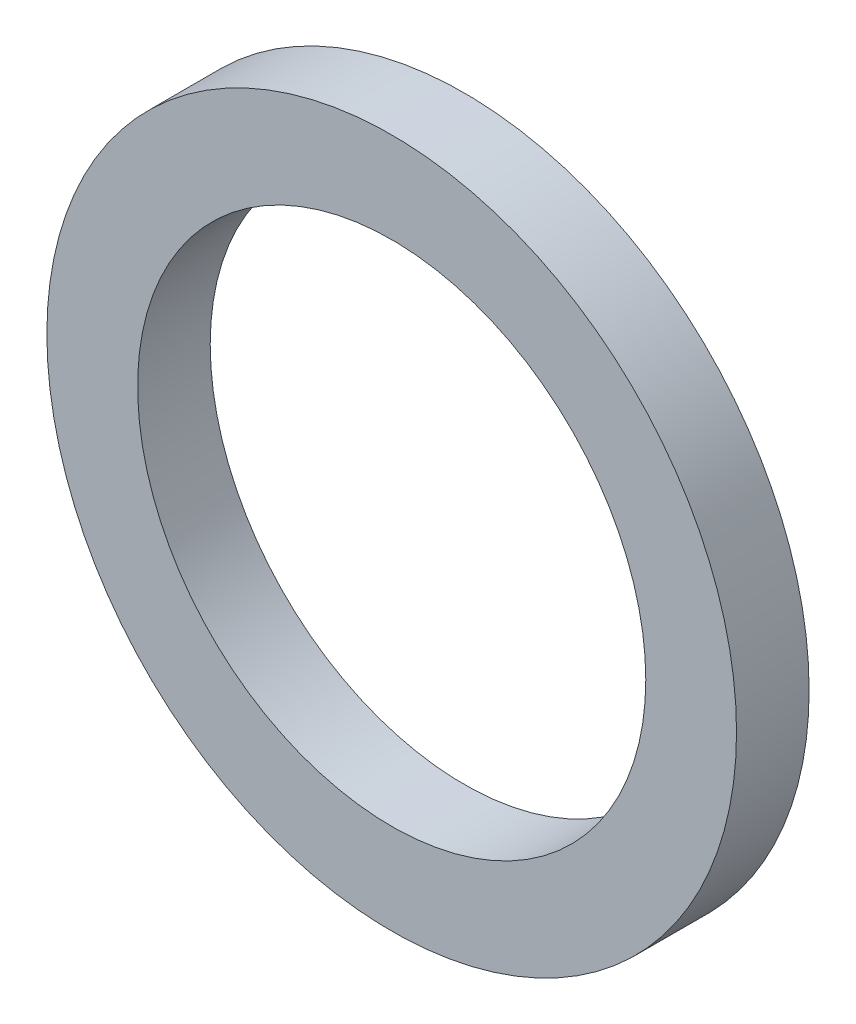
SolidWorks part; units mm, degrees
ref_plane "Plan de face" through (0, 0, 0) normal (0, 0, 1) x (1, 0, 0)
ref_plane "Plan de dessus" through (0, 0, 0) normal (0, 1, 0) x (1, 0, 0)
ref_plane "Plan de droite" through (0, 0, 0) normal (1, 0, 0) x (0, 0, -1)
sketch "Esquisse1" plane through (0, 0, 0) normal (0, 0, 1) x (1, 0, 0)
  circle A0 centre (0, 0) radius 48.5
  dimension "D1" = 97
extrude "Boss.-Extru.1" add sketch "Esquisse1" along normal blind 70
sketch "Esquisse2" plane through (0, 0, 70) normal (0, 0, 1) x (1, 0, 0)
  circle A0 centre (0, 0) radius 48.5
  circle A1 centre (0, 0) radius 47.5
  dimension "D1" = 95
extrude "Enlèv. mat.-Extru.1" cut sketch "Esquisse2" against normal blind 10
sketch "Esquisse3" plane through (0, 0, 70) normal (0, 0, 1) x (1, 0, 0)
  circle A0 centre (0, 0) radius 35
  dimension "D1" = 70
extrude "Enlèv. mat.-Extru.2" cut sketch "Esquisse3" against normal through all
sketch "Esquisse5" plane through (0, 0, 0) normal (0, 0, -1) x (-1, 0, 0)
  circle A0 centre (0, 0) radius 37
  circle A1 centre (0, 0) radius 45
  circle A2 centre (0, 0) radius 35 construction
  dimension "D1" = 8
  dimension "D2" = 2
extrude "Enlèv. mat.-Extru.3" cut sketch "Esquisse5" against normal blind 68
sketch "Esquisse6" plane through (0, 0, 0) normal (0, 0, -1) x (-1, 0, 0)
  line L5 (-10, -48.5543) -> (10, -48.5543)
  line L6 (-10, -48.5543) -> (-10, -43.8748)
  line L7 (-10, -43.8748) -> (10, -43.8748)
  line L8 (10, -48.5543) -> (10, -43.8748)
  circle A1 centre (0, 0) radius 45 construction
  dimension "D1" = 20
  dimension "D2" = 10
extrude "Enlèv. mat.-Extru.5" cut sketch "Esquisse6" against normal blind 68
sketch "Esquisse8" plane through (0, 0, 0) normal (0, 0, -1) x (-1, 0, 0)
  line L0 (48.5, 0) -> (-48.5, 0) construction
  line L1 (0, 0) -> (31.8198, -31.8198) construction
  line L2 (0, 0) -> (31.8198, 31.8198) construction
  line L3 (34.2947, 34.2947) -> (31.8198, 31.8198)
  line L4 (34.2947, -34.2947) -> (31.8198, -31.8198)
  line L5 (0, 0) -> (0, -37) construction
  line L6 (-34.2947, -34.2947) -> (-31.8198, -31.8198)
  line L7 (-34.2947, 34.2947) -> (-31.8198, 31.8198)
  arc A0 (10, -47.4579) -> (-10, -47.4579) centre (0, 0) ccw construction
  arc A1 (10, -43.8748) -> (-10, -43.8748) centre (0, 0) ccw construction
  arc A2 (31.8198, -31.8198) -> (31.8198, 31.8198) centre (0, 0) ccw
  arc A3 (34.2947, -34.2947) -> (34.2947, 34.2947) centre (0, 0) ccw
  circle A4 centre (0, 0) radius 37 construction
  arc A5 (-31.8198, -31.8198) -> (-31.8198, 31.8198) centre (0, 0) cw
  arc A6 (-34.2947, -34.2947) -> (-34.2947, 34.2947) centre (0, 0) cw
  arc M16 (10, -47.4579) -> (-10, -47.4579) centre (0, 0) ccw
  arc M18 (-10, -43.8748) -> (10, -43.8748) centre (0, 0) cw
  dimension "D1" = 45
  dimension "D2" = 45
extrude "Boss.-Extru.2" add sketch "Esquisse8" along normal blind 10 contours L4 L3 M16 M18 | A6 L7 A5 L6
sketch "Esquisse9" plane through (0, 0, 0) normal (0, 1, 0) x (1, 0, 0)
  line L1 (-48.5, -60) -> (48.582, -60)
  line L2 (-48.5, -60) -> (-48.5, 23.8127)
  line L3 (-48.5, 23.8127) -> (48.582, 23.8127)
  line L4 (48.582, -60) -> (48.582, 23.8127)
extrude "Enlèv. mat.-Extru.6" cut sketch "Esquisse9" along normal through all both and the other way through all
